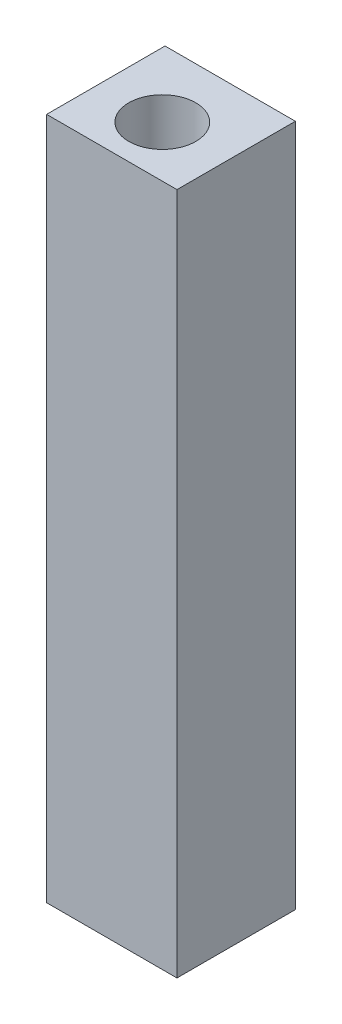
SolidWorks part; units mm, degrees
material "Titanium"
ref_plane "Front Plane" through (0, 0, 0) normal (0, 0, 1) x (1, 0, 0)
ref_plane "Top Plane" through (0, 0, 0) normal (0, 1, 0) x (1, 0, 0)
ref_plane "Right Plane" through (0, 0, 0) normal (1, 0, 0) x (0, 0, -1)
sketch "Sketch1" plane through (0, 0, 0) normal (0, 1, 0) x (1, 0, 0)
  line L1 (-25.4065, 17.341) -> (-6.318, 17.341)
  line L2 (-25.4065, 17.341) -> (-25.4065, 0)
  line L3 (-25.4065, 0) -> (-6.318, 0)
  line L4 (-6.318, 17.341) -> (-6.318, 0)
extrude "Boss-Extrude1" add sketch "Sketch1" along normal blind 100
sketch "Sketch2" plane through (0, 100, 0) normal (0, 1, 0) x (1, 0, 0)
  circle A0 centre (-15.954, 7.4863) radius 4.9096
extrude "Cut-Extrude1" cut sketch "Sketch2" against normal blind 10
